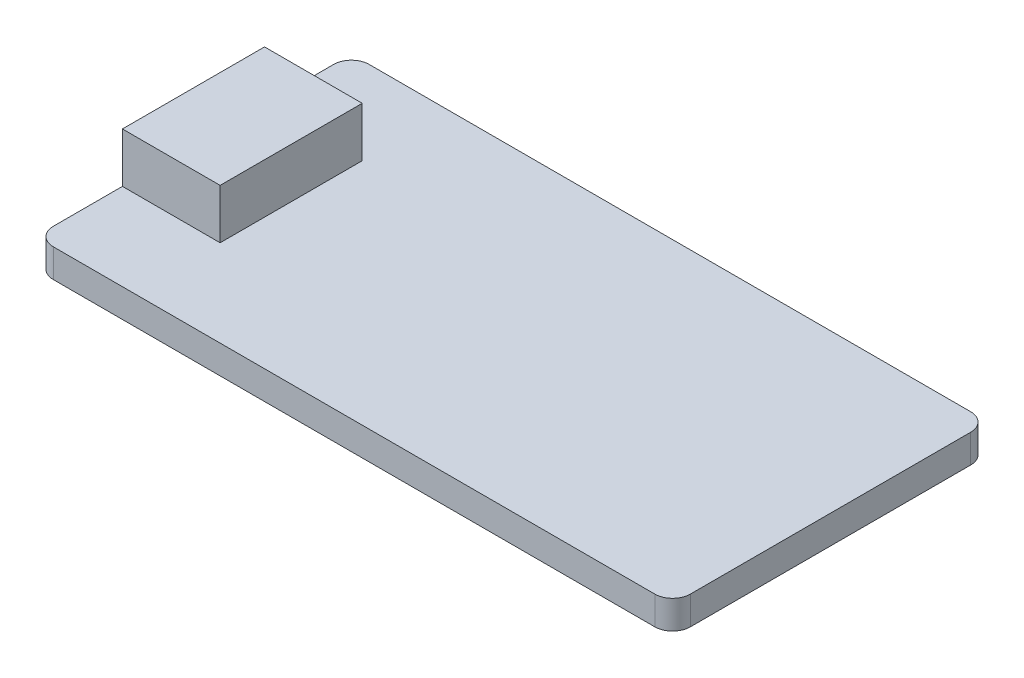
SolidWorks part; units mm, degrees
ref_plane "Front Plane" through (0, 0, 0) normal (0, 0, 1) x (1, 0, 0)
ref_plane "Top Plane" through (0, 0, 0) normal (0, 1, 0) x (1, 0, 0)
ref_plane "Right Plane" through (0, 0, 0) normal (1, 0, 0) x (0, 0, -1)
sketch "Sketch1" plane through (0, 0, 0) normal (0, 1, 0) x (1, 0, 0)
  line L1 (0, 0) -> (35.86, 0)
  line L2 (0, 0) -> (0, 17.78)
  line L3 (0, 17.78) -> (35.86, 17.78)
  line L4 (35.86, 0) -> (35.86, 17.78)
  dimension "D1" = 35.86
  dimension "D2" = 17.78
extrude "Boss-Extrude1" add sketch "Sketch1" along normal blind 1.6
sketch "Sketch2" plane through (0, 1.6, 0) normal (0, 1, 0) x (1, 0, 0)
  line L0 (0, 17.78) -> (0, 0) construction
  line L1 (0, 12.89) -> (5.5, 12.89)
  line L2 (0, 12.89) -> (0, 4.89)
  line L3 (0, 4.89) -> (5.5, 4.89)
  line L4 (5.5, 12.89) -> (5.5, 4.89)
  line L5 (35.86, 8.89) -> (5.5, 8.89) construction
  line L6 (35.86, 0) -> (35.86, 17.78) construction
  dimension "D1" = 5.5
  dimension "D2" = 8
extrude "Boss-Extrude2" add sketch "Sketch2" along normal blind 2.8 contours L1 L4 L3 L2
fillet "Fillet1" radius 1 4 edges at (0, 0.8, -17.78) (35.86, 0.8, -17.78) (35.86, 0.8, 0) (0, 0.8, 0)
